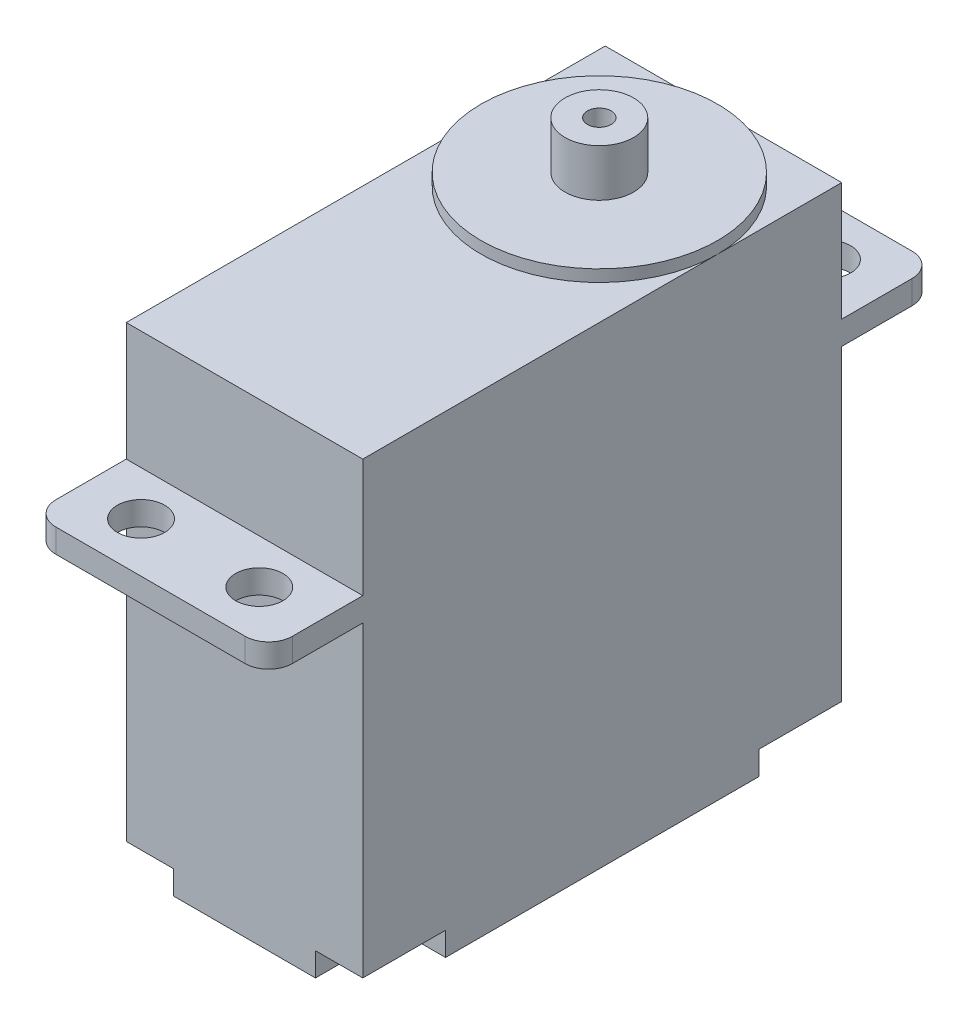
SolidWorks part; units mm, degrees
ref_plane "Front Plane" through (0, 0, 0) normal (0, 0, 1) x (1, 0, 0)
ref_plane "Top Plane" through (0, 0, 0) normal (0, 1, 0) x (1, 0, 0)
ref_plane "Right Plane" through (0, 0, 0) normal (1, 0, 0) x (0, 0, -1)
sketch "Sketch2" plane through (0, 77, 0) normal (0, 1, 0) x (1, 0, 0)
  line L1 (-49.2826, 255.8952) -> (-29.2826, 255.8952)
  line L2 (-49.2826, 255.8952) -> (-49.2826, 296.3952)
  line L3 (-49.2826, 296.3952) -> (-29.2826, 296.3952)
  line L4 (-29.2826, 255.8952) -> (-29.2826, 296.3952)
  dimension "D1" = 40.5
  dimension "D2" = 20
extrude "Boss-Extrude1" add sketch "Sketch2" along normal blind 28
sketch "Sketch3" plane through (0, 105, 0) normal (0, 1, 0) x (1, 0, 0)
  line L0 (-49.2826, 296.3952) -> (-49.2826, 255.8952) construction
  line L1 (-49.2826, 247.9452) -> (-29.2826, 247.9452)
  line L2 (-49.2826, 247.9452) -> (-49.2826, 304.3452)
  line L3 (-49.2826, 304.3452) -> (-29.2826, 304.3452)
  line L4 (-29.2826, 247.9452) -> (-29.2826, 304.3452)
  line L5 (-29.2826, 255.8952) -> (-29.2826, 296.3952) construction
  line L6 (-39.2826, 255.8952) -> (-39.2826, 296.3952) construction
  line L7 (-49.2826, 255.8952) -> (-29.2826, 255.8952) construction
  line L8 (-29.2826, 296.3952) -> (-49.2826, 296.3952) construction
  line L9 (-39.2826, 276.1452) -> (-34.2441, 276.1452) construction
  dimension "D1" = 0
  dimension "D2" = 0
  dimension "D3" = 56.4
  dimension "D4" = 28.2
extrude "Boss-Extrude2" add sketch "Sketch3" along normal blind 2
sketch "Sketch4" plane through (0, 107, 0) normal (0, 1, 0) x (1, 0, 0)
  line L4 (-49.2826, 296.3952) -> (-49.2826, 255.8952)
  line L5 (-29.2826, 296.3952) -> (-49.2826, 296.3952)
  line L6 (-29.2826, 255.8952) -> (-29.2826, 296.3952)
  line L7 (-49.2826, 255.8952) -> (-29.2826, 255.8952)
  line L8 (-49.2826, 296.3952) -> (-49.2826, 255.8952)
  line L9 (-29.2826, 296.3952) -> (-49.2826, 296.3952)
  line L10 (-29.2826, 255.8952) -> (-29.2826, 296.3952)
  line L11 (-49.2826, 255.8952) -> (-29.2826, 255.8952)
  dimension "D1" = 0
extrude "Boss-Extrude3" add sketch "Sketch4" along normal blind 10
sketch "Sketch5" plane through (0, 117, 0) normal (0, 1, 0) x (1, 0, 0)
  line L0 (-29.2826, 255.8952) -> (-29.2826, 296.3952) construction
  line L1 (-49.2826, 296.3952) -> (-49.2826, 255.8952) construction
  line L2 (-49.2826, 255.8952) -> (-29.2826, 255.8952) construction
  circle A0 centre (-39.2826, 285.8952) radius 10
  dimension "D1" = 30
extrude "Boss-Extrude4" add sketch "Sketch5" along normal blind 1
sketch "Sketch6" plane through (0, 118, 0) normal (0, 1, 0) x (1, 0, 0)
  circle A0 centre (-39.2826, 285.8952) radius 2.9
  circle A1 centre (-39.2826, 285.8952) radius 1
extrude "Boss-Extrude5" add sketch "Sketch6" along normal blind 4
sketch "Sketch7" plane through (0, 107, 0) normal (0, 1, 0) x (1, 0, 0)
  circle A0 centre (-44.2826, 252.1452) radius 2
  circle A1 centre (-34.2826, 252.1452) radius 2
  circle A2 centre (-34.2826, 300.1452) radius 2
  circle A3 centre (-44.2826, 300.1452) radius 2
extrude "Cut-Extrude1" cut sketch "Sketch7" against normal blind 2
fillet "Fillet1" radius 2
sketch "Sketch8" plane through (0, 77, 0) normal (0, -1, 0) x (1, 0, 0)
  line L0 (-39.2826, -255.8952) -> (-39.2826, -296.3952) construction
  line L1 (-29.2826, -255.8952) -> (-33.2826, -255.8952)
  line L2 (-29.2826, -255.8952) -> (-29.2826, -262.8952)
  line L3 (-29.2826, -262.8952) -> (-33.2826, -262.8952)
  line L4 (-33.2826, -255.8952) -> (-33.2826, -262.8952)
  line L5 (-49.2826, -255.8952) -> (-29.2826, -255.8952) construction
  line L6 (-29.2826, -296.3952) -> (-49.2826, -296.3952) construction
  line L7 (-29.2826, -276.1452) -> (-49.2826, -276.1452) construction
  line L8 (-29.2826, -255.8952) -> (-29.2826, -296.3952) construction
  line L9 (-49.2826, -296.3952) -> (-49.2826, -255.8952) construction
  line L10 (-33.2826, -296.3952) -> (-33.2826, -289.3952)
  line L11 (-29.2826, -289.3952) -> (-33.2826, -289.3952)
  line L12 (-29.2826, -296.3952) -> (-29.2826, -289.3952)
  line L13 (-29.2826, -296.3952) -> (-33.2826, -296.3952)
  line L14 (-49.2826, -296.3952) -> (-45.2826, -296.3952)
  line L15 (-49.2826, -296.3952) -> (-49.2826, -289.3952)
  line L16 (-49.2826, -289.3952) -> (-45.2826, -289.3952)
  line L17 (-45.2826, -296.3952) -> (-45.2826, -289.3952)
  line L18 (-45.2826, -255.8952) -> (-45.2826, -262.8952)
  line L19 (-49.2826, -262.8952) -> (-45.2826, -262.8952)
  line L20 (-49.2826, -255.8952) -> (-49.2826, -262.8952)
  line L21 (-49.2826, -255.8952) -> (-45.2826, -255.8952)
extrude "Cut-Extrude2" cut sketch "Sketch8" against normal blind 2
sketch "Sketch9" plane through (0, 0, -296.3952) normal (0, 0, -1) x (-1, 0, 0)
  line L0 (33.2826, 77) -> (45.2826, 77) construction
  line L1 (35.2826, 77) -> (43.2826, 77)
  line L2 (35.2826, 77) -> (35.2826, 80)
  line L3 (35.2826, 80) -> (43.2826, 80)
  line L4 (43.2826, 77) -> (43.2826, 80)
  line L5 (39.2826, 122) -> (39.2826, 77) construction
  line L6 (42.1826, 122) -> (36.3826, 122) construction
  dimension "D1" = 8
  dimension "D2" = 4
  dimension "D3" = 3
extrude "Boss-Extrude6" add sketch "Sketch9" along normal blind 5
ref_plane "Plane1" through (0, 124, 0) normal (0, 1, 0) x (1, 0, 0)
